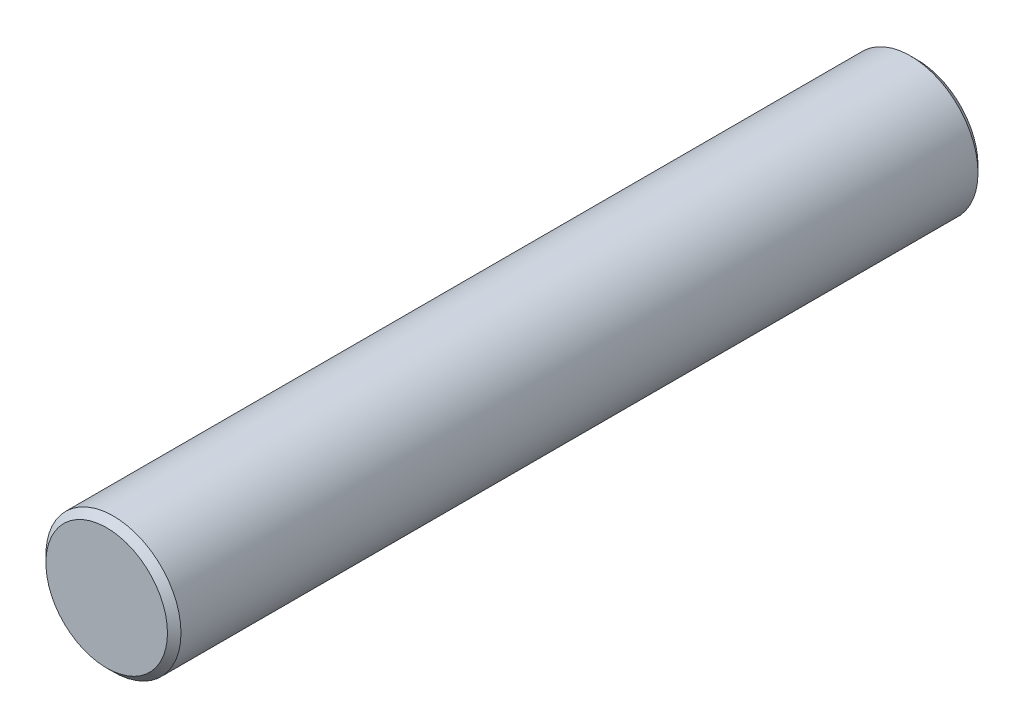
SolidWorks part; units mm, degrees
material "Stainless Steel (ferritic)"
ref_plane "Front Plane" through (0, 0, 0) normal (0, 0, 1) x (1, 0, 0)
ref_plane "Top Plane" through (0, 0, 0) normal (0, 1, 0) x (1, 0, 0)
ref_plane "Right Plane" through (0, 0, 0) normal (1, 0, 0) x (0, 0, -1)
sketch "Sketch1" plane through (0, 0, 0) normal (0, 0, 1) x (1, 0, 0)
  circle A0 centre (0, 0) radius 1
  point P4 (0, 0)
  dimension "D1" = 2
extrude "Boss-Extrude1" add sketch "Sketch1" along normal blind 12
chamfer "Chamfer1" distance 0.1 angle 45 2 edges at (1, 0, 0) (1, 0, 12)
